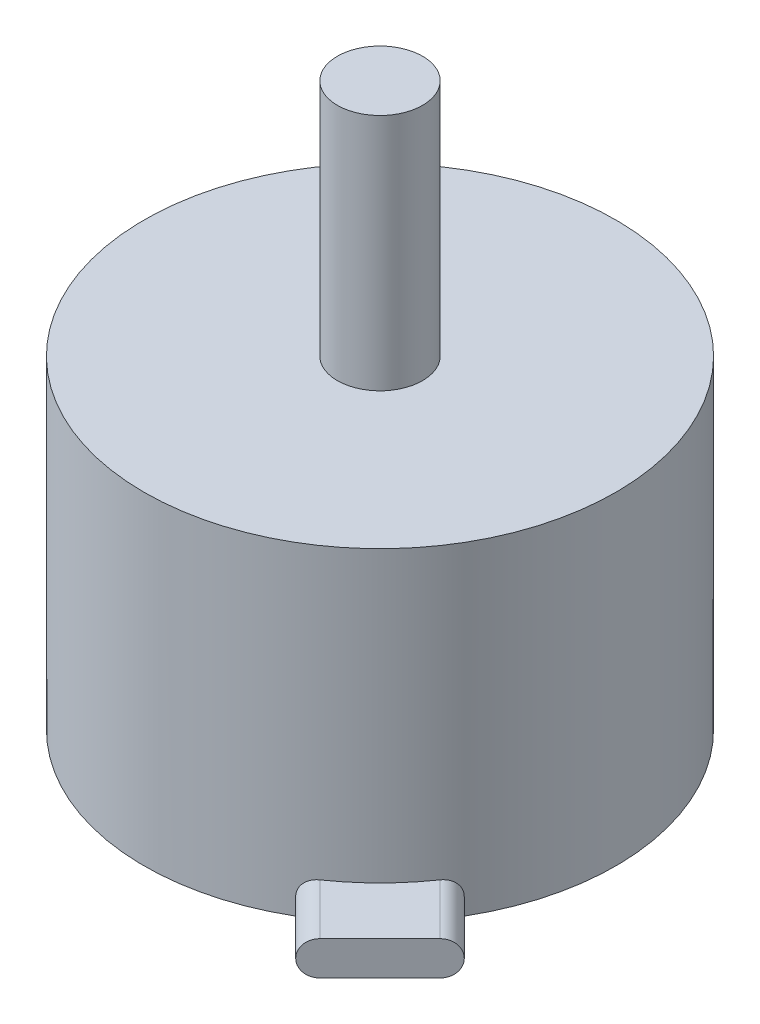
SolidWorks part; units mm, degrees
ref_plane "Front Plane" through (0, 0, 0) normal (0, 0, 1) x (1, 0, 0)
ref_plane "Top Plane" through (0, 0, 0) normal (0, 1, 0) x (1, 0, 0)
ref_plane "Right Plane" through (0, 0, 0) normal (1, 0, 0) x (0, 0, -1)
sketch "Sketch1" plane through (0, 0, 0) normal (0, 1, 0) x (1, 0, 0)
  circle A0 centre (0, 0) radius 13.85
  dimension "D1" = 27.7
extrude "Boss-Extrude1" add sketch "Sketch1" along normal blind 19
sketch "Sketch2" plane through (0, 19, 0) normal (0, 1, 0) x (1, 0, 0)
  circle A0 centre (0, 0) radius 2.5
  dimension "D1" = 5
extrude "Boss-Extrude2" add sketch "Sketch2" along normal blind 14
sketch "Sketch3" plane through (0, 0, 0) normal (0, -1, 0) x (1, 0, 0)
  circle A0 centre (0, 0) radius 8
  circle A1 centre (0, 0) radius 9.5
  point P4 (0, 8)
  point P5 (0, -8)
  point P6 (9.5, 0)
  point P7 (-9.5, 0)
  dimension "D1" = 16
  dimension "D2" = 19
hole_wizard "M3x0.5 Tapped Hole1" positions "Sketch4" profile "Sketch5" tap size "M3x0.5" standard "ANSI Metric"
sketch "Sketch4" plane through (0, 0, 0) normal (0, -1, 0) x (-1, 0, 0)
  point P0 (0, -8)
  point P3 (9.5, 0)
  point P6 (0, 8)
  point P9 (-9.5, 0)
sketch "Sketch5" plane through (0, 0, 8) normal (1, 0, 0) x (0, 0, -1)
  line L0 (0, 0) -> (0, 8.2511)
  line L1 (0, 8.2511) -> (1.25, 7.5)
  line L2 (1.25, 7.5) -> (1.25, 0)
  line L5 (1.25, 0) -> (0, 0)
  line L10 (0, 8.2511) -> (-1.25, 7.5) construction
  line L11 (0, -6.35) -> (0, 107.95) construction
  dimension "Tap Drill Dia." = 2.5
  dimension "Tap Drill Depth" = 7.5
  dimension "Drill Angle" = 118
cosmetic thread "Hole Thread1" parameters "D1"=6, "D2"=3
cosmetic thread "Hole Thread2" parameters "D1"=6, "D2"=3
cosmetic thread "Hole Thread3" parameters "D1"=6, "D2"=3
cosmetic thread "Hole Thread4" parameters "D1"=6, "D2"=3
sketch "Sketch6" plane through (0, 0, 0) normal (0, -1, 0) x (1, 0, 0)
  line L0 (0, -8) -> (0, 8) construction
  line L1 (-9.5, 0) -> (9.5, 0) construction
  line L2 (0, 0) -> (9.7934, 9.7934) construction
  circle A0 centre (0, 0) radius 13.85 construction
  point P11 (9.7934, 9.7934)
  dimension "D1" = 45
ref_plane "Plane1" through (9.7934, 0, 9.7934) normal (0.7071, 0, 0.7071) x (0.7071, 0, -0.7071)
sketch "Sketch7" plane through (9.7934, 0, 9.7934) normal (0.7071, 0, 0.7071) x (0.7071, 0, -0.7071)
  line L0 (-2.5, 1) -> (2.5, 1) construction
  line L1 (-2.5, 2) -> (2.5, 2)
  line L2 (-2.5, 0) -> (2.5, 0)
  line L3 (5.6569, 0) -> (-5.6569, 0) construction
  arc A0 (-2.5, 2) -> (-2.5, 0) centre (-2.5, 1) ccw
  arc A1 (2.5, 0) -> (2.5, 2) centre (2.5, 1) ccw
  point P2 (0, 1)
  point P7 (0, 0)
  point P8 (0, 0)
  point P9 (0.5223, 0.7964)
  dimension "D2" = 5
  dimension "D1" = 2
extrude "Boss-Extrude3" add sketch "Sketch7" along normal blind 4 and the other way up to next contours L1 A1 L2 A0
